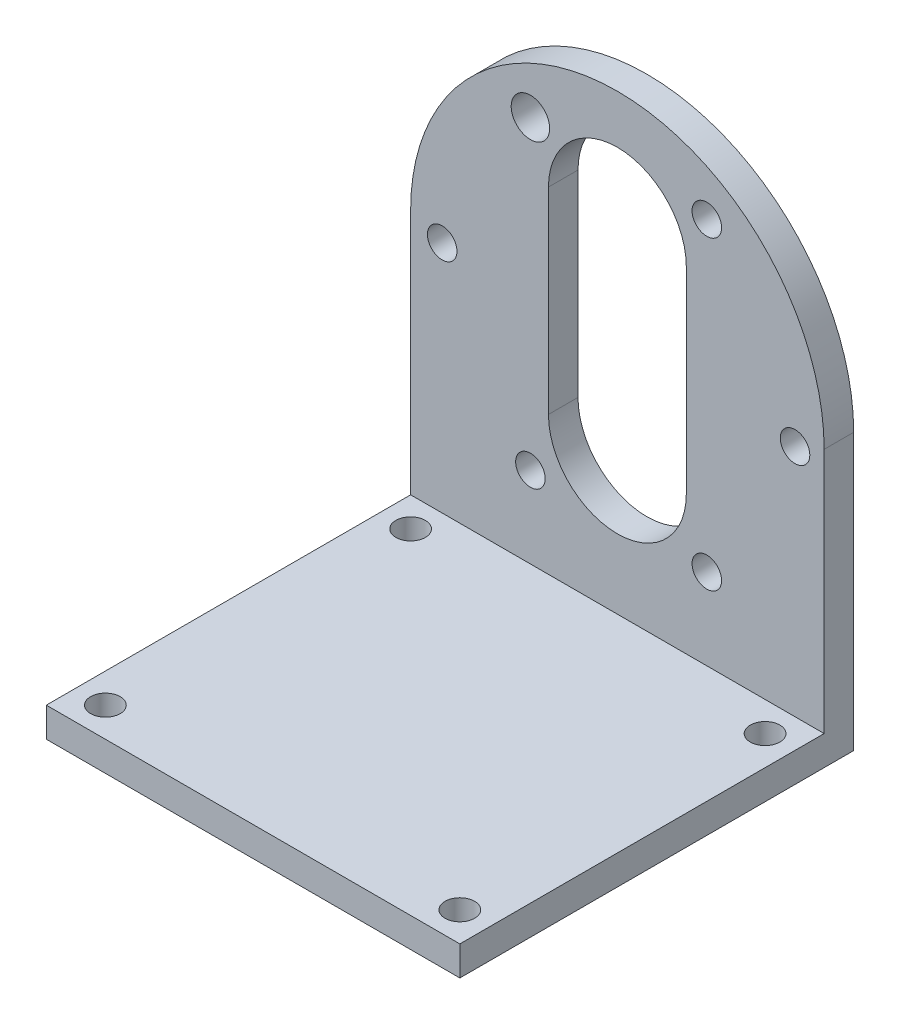
SolidWorks part; units mm, degrees
ref_plane "前视基准面" through (0, 0, 0) normal (0, 0, 1) x (1, 0, 0)
ref_plane "上视基准面" through (0, 0, 0) normal (0, 1, 0) x (1, 0, 0)
ref_plane "右视基准面" through (0, 0, 0) normal (1, 0, 0) x (0, 0, -1)
sketch "草图4" plane through (0, 0, 0) normal (0, 1, 0) x (1, 0, 0)
  line L1 (-21, -21) -> (21, -21)
  line L2 (-21, -21) -> (-21, 19)
  line L3 (-21, 19) -> (21, 19)
  line L4 (21, -21) -> (21, 19)
  point P7 (-0.8889, 22.6111)
  dimension "D1" = 21
  dimension "D2" = 21
  dimension "D3" = 40
extrude "凸台-拉伸1" add sketch "草图4" along normal blind 3
sketch "草图9" plane through (-21, 0, 0) normal (-1, 0, 0) x (0, 0, 1)
  line L0 (-19, 3) -> (-19, 28)
extrude "拉伸-薄壁3" add sketch "草图9" against normal blind 42 thin
sketch "草图10" plane through (0, 0, -16) normal (0, 0, 1) x (1, 0, 0)
  line L0 (21, 28) -> (-21, 28) construction
  circle A0 centre (0, 28) radius 21
extrude "凸台-拉伸2" add sketch "草图10" against normal blind 3 contours A0
sketch "草图11" plane through (0, 0, -16) normal (0, 0, 1) x (1, 0, 0)
  line L0 (-7, 37.0683) -> (-7, 17.0683)
  line L1 (7, 37.0683) -> (7, 17.0683)
  arc A0 (7, 37.0683) -> (-7, 37.0683) centre (0, 37.0683) ccw
  arc A1 (-7, 17.0683) -> (7, 17.0683) centre (0, 17.0683) ccw
  point P8 (0, 0)
  point P9 (0, 0)
extrude "切除-拉伸6" cut sketch "草图11" against normal blind 3
sketch "草图14" plane through (0, 0, -16) normal (0, 0, 1) x (1, 0, 0)
  line L1 (9.0843, 42.2794) -> (-8.8327, 42.2794) construction
  line L2 (-8.8327, 42.2794) -> (-17.7912, 26.7628) construction
  line L3 (-17.7912, 26.7628) -> (-8.8327, 11.2463) construction
  line L4 (-8.8327, 11.2463) -> (9.0843, 11.2463) construction
  line L5 (9.0843, 11.2463) -> (18.0428, 26.7628) construction
  line L6 (18.0428, 26.7628) -> (9.0843, 42.2794) construction
  circle A0 centre (0.1258, 26.7628) radius 15.5166 construction
  circle A2 centre (-8.8327, 42.2794) radius 1.9523
sketch "草图15" plane through (0, 0, -16) normal (0, 0, 1) x (1, 0, 0)
sketch "草图16" plane through (0, 0, -16) normal (0, 0, 1) x (1, 0, 0)
  circle A0 centre (-8.8327, 42.2794) radius 1.5
  circle A1 centre (-17.7912, 26.7628) radius 1.5
  circle A2 centre (-8.8327, 11.2463) radius 1.5
  circle A3 centre (9.0843, 11.2463) radius 1.5
  circle A4 centre (18.0428, 26.7628) radius 1.5
  circle A6 centre (9.0843, 42.2794) radius 1.5
extrude "切除-拉伸7" cut sketch "草图16" against normal blind 3
extrude "切除-拉伸8" cut sketch "草图14" against normal blind 3
sketch "草图17" plane through (0, 3, 0) normal (0, 1, 0) x (1, 0, 0)
  line L0 (21, 16) -> (-21, 16) construction
  line L1 (-18, 13) -> (18, 13) construction
  line L2 (-18, 13) -> (-18, -18) construction
  line L3 (-18, -18) -> (18, -18) construction
  line L4 (18, 13) -> (18, -18) construction
  line L5 (-21, -21) -> (21, -21) construction
  line L6 (-21, 16) -> (-21, -21) construction
  circle A0 centre (-18, 13) radius 1.5
  circle A1 centre (18, 13) radius 1.5
  circle A2 centre (-18, -18) radius 1.5
  circle A3 centre (18, -18) radius 1.5
  dimension "D1" = 3
  dimension "D2" = 36
  dimension "D3" = 3
  dimension "D4" = 3
extrude "切除-拉伸10" cut sketch "草图17" against normal blind 3
